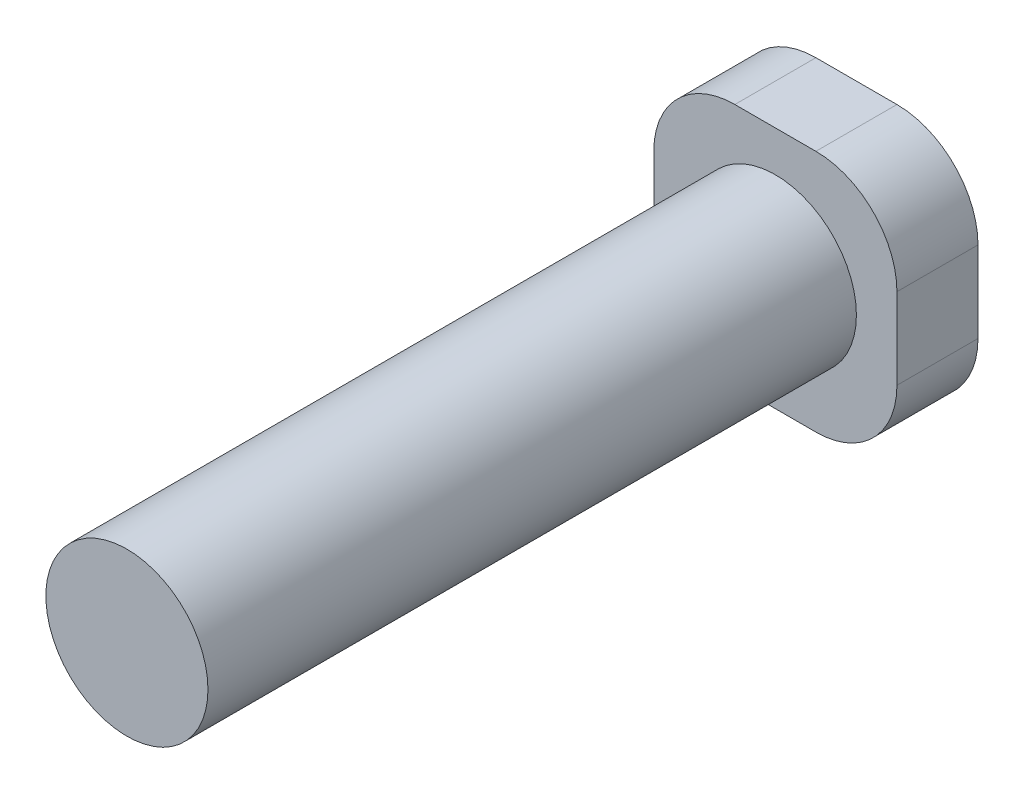
SolidWorks part; units mm, degrees
material "AISI 4130 Steel, normalized at 870C"
ref_plane "Front Plane" through (0, 0, 0) normal (0, 0, 1) x (1, 0, 0)
ref_plane "Top Plane" through (0, 0, 0) normal (0, 1, 0) x (1, 0, 0)
ref_plane "Right Plane" through (0, 0, 0) normal (1, 0, 0) x (0, 0, -1)
sketch "Sketch1" plane through (0, 0, 0) normal (0, 0, 1) x (1, 0, 0)
  line L1 (-0.5, -1.5) -> (0.5, -1.5)
  line L2 (-1.5, -0.5) -> (-1.5, 0.5)
  line L3 (-0.5, 1.5) -> (0.5, 1.5)
  line L4 (1.5, -0.5) -> (1.5, 0.5)
  line L5 (-1.5, -1.5) -> (1.5, 1.5) construction
  line L6 (-1.5, 1.5) -> (1.5, -1.5) construction
  arc A1 (0.5, -1.5) -> (1.5, -0.5) centre (0.5, -0.5) ccw
  arc A2 (0.5, 1.5) -> (1.5, 0.5) centre (0.5, 0.5) cw
  arc A3 (-0.5, -1.5) -> (-1.5, -0.5) centre (-0.5, -0.5) cw
  arc A4 (-1.5, 0.5) -> (-0.5, 1.5) centre (-0.5, 0.5) cw
  point P0 (0, 0)
  dimension "D4" = 1
  dimension "D1" = 3
  dimension "D2" = 3
extrude "Boss-Extrude2" add sketch "Sketch1" along normal blind 1
sketch "Sketch2" plane through (0, 0, 1) normal (0, 0, 1) x (1, 0, 0)
  circle A0 centre (0, 0) radius 1
  dimension "D1" = 2
extrude "Boss-Extrude3" add sketch "Sketch2" along normal blind 8
